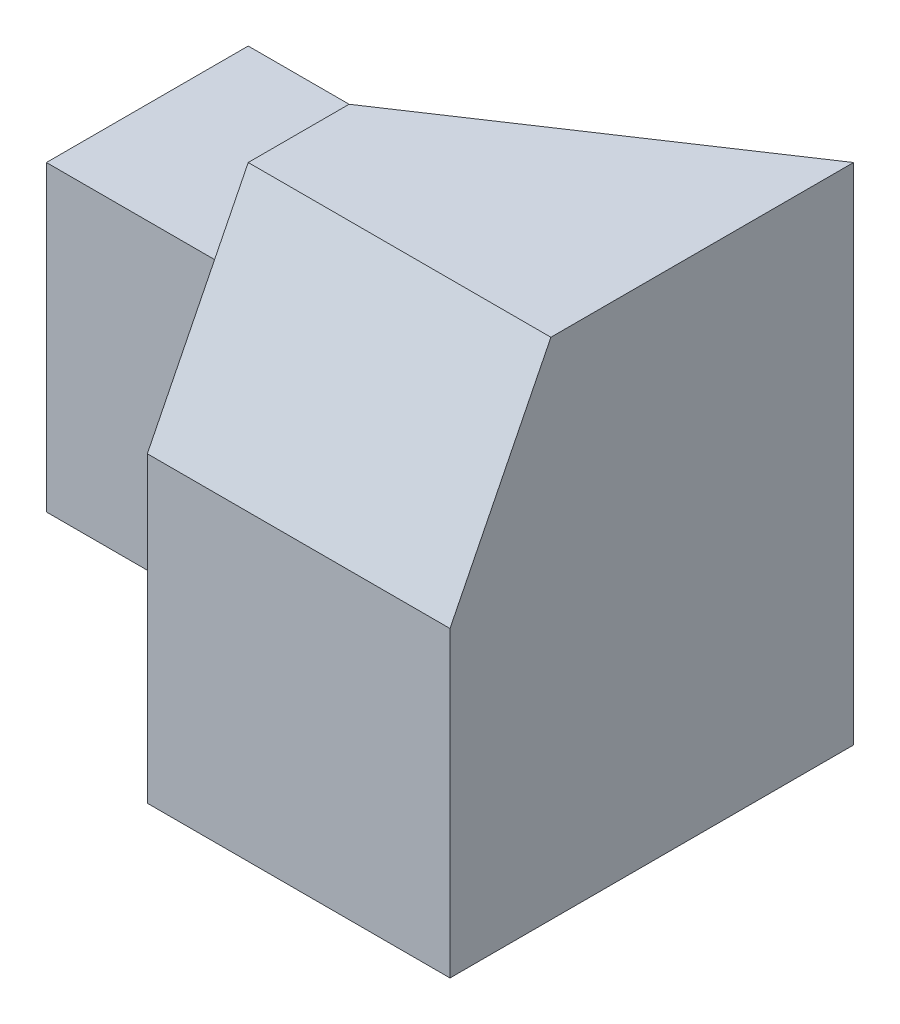
SolidWorks part; units mm, degrees
ref_plane "Front Plane" through (0, 0, 0) normal (0, 0, 1) x (1, 0, 0)
ref_plane "Top Plane" through (0, 0, 0) normal (0, 1, 0) x (1, 0, 0)
ref_plane "Right Plane" through (0, 0, 0) normal (1, 0, 0) x (0, 0, -1)
sketch "Sketch1" plane through (0, 0, 0) normal (0, 0, 1) x (1, 0, 0)
  line L1 (0, 0) -> (30, 0)
  line L2 (0, 0) -> (0, 25)
  line L3 (0, 25) -> (30, 25)
  line L4 (30, 0) -> (30, 25)
  dimension "D1" = 30
  dimension "D2" = 25
extrude "Boss-Extrude1" add sketch "Sketch1" along normal blind 20
sketch "Sketch2" plane through (0, 0, 20) normal (0, 0, 1) x (1, 0, 0)
  line L0 (30, 25) -> (0, 25) construction
  line L1 (0, 0) -> (15, 0)
  line L2 (0, 0) -> (0, 25)
  line L3 (0, 25) -> (15, 25)
  line L4 (15, 0) -> (15, 25)
extrude "Cut-Extrude1" cut sketch "Sketch2" against normal blind 10
sketch "Sketch3" plane through (0, 0, 10) normal (0, 0, 1) x (1, 0, 0)
  line L0 (15, 0) -> (15, 25) construction
  line L1 (0, 25) -> (15, 25)
  line L2 (0, 25) -> (0, 15)
  line L3 (0, 15) -> (15, 15)
  line L4 (15, 25) -> (15, 15)
  dimension "D1" = 10
extrude "Cut-Extrude2" cut sketch "Sketch3" against normal blind 10
sketch "Sketch4" plane through (15, 0, 0) normal (-1, 0, 0) x (0, 0, 1)
  line L0 (15, 25) -> (20, 15)
  line L1 (0, 25) -> (20, 25) construction
  line L2 (20, 0) -> (20, 25) construction
  line L3 (20, 15) -> (20, 25)
  line L4 (20, 25) -> (15, 25)
  dimension "D1" = 10
  dimension "D2" = 5
extrude "Cut-Extrude3" cut sketch "Sketch4" against normal blind 20
sketch "Sketch5" plane through (0, 25, 0) normal (0, 1, 0) x (1, 0, 0)
  line L0 (15, -10) -> (30, 0)
  line L1 (30, 0) -> (15, 0)
  line L2 (15, 0) -> (15, -10)
extrude "Cut-Extrude4" cut sketch "Sketch5" against normal blind 10
